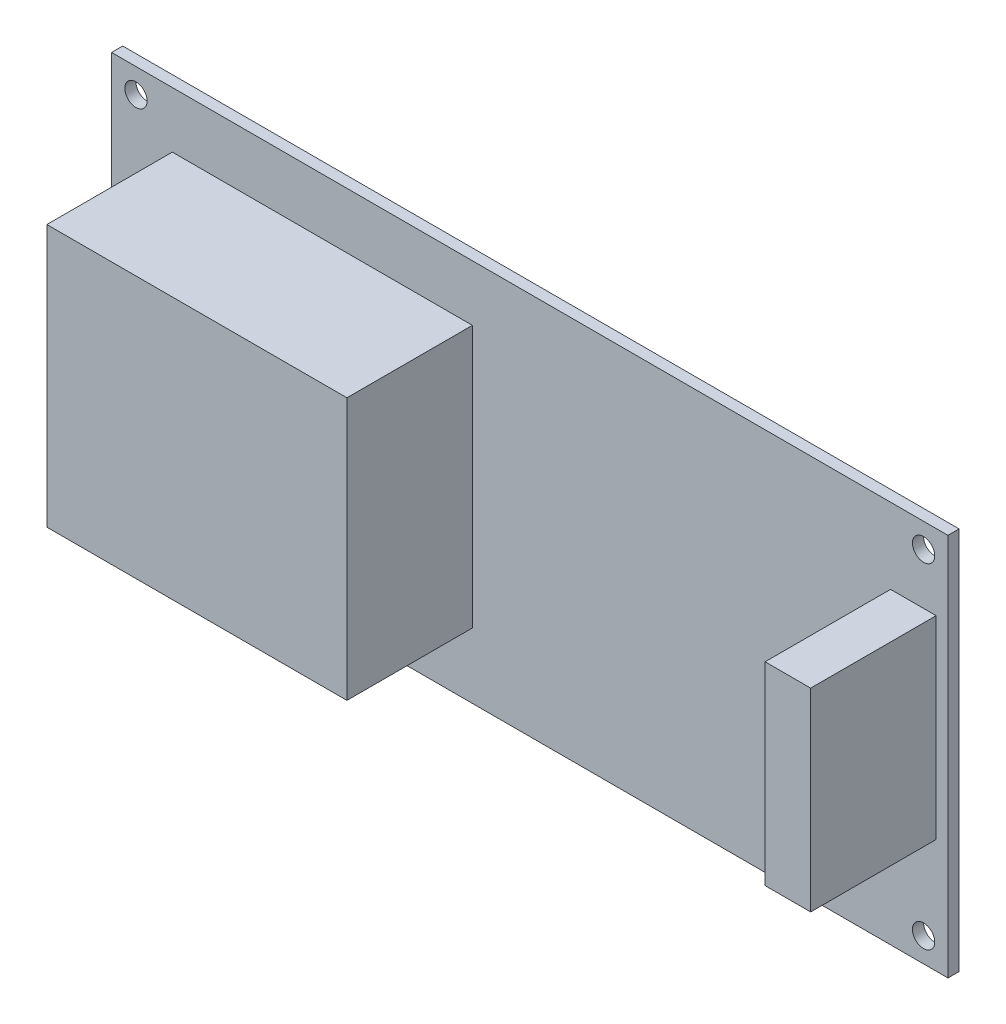
SolidWorks part; units mm, degrees
ref_plane "Plan de face" through (0, 0, 0) normal (0, 0, 1) x (1, 0, 0)
ref_plane "Plan de dessus" through (0, 0, 0) normal (0, 1, 0) x (1, 0, 0)
ref_plane "Plan de droite" through (0, 0, 0) normal (1, 0, 0) x (0, 0, -1)
sketch "Esquisse1" plane through (0, 0, 0) normal (0, 0, 1) x (1, 0, 0)
  line L0 (-56.5, 24) -> (56.5, -24) construction
  line L1 (-60, 27.5) -> (60, 27.5)
  line L2 (-60, 27.5) -> (-60, -27.5)
  line L3 (-60, -27.5) -> (60, -27.5)
  line L4 (60, 27.5) -> (60, -27.5)
  circle A0 centre (-56.5, 24) radius 1.6
  circle A1 centre (56.5, 24) radius 1.6
  circle A2 centre (56.5, -24) radius 1.6
  circle A3 centre (-56.5, -24) radius 1.6
  point P12 (0, 27.5)
  point P14 (-60, 0)
  point P15 (0, 0)
  point P16 (0, 0)
  point P17 (0, 0)
  point P18 (0, 0)
  point P19 (0, 0)
  point P20 (0, 0)
  dimension "D3" = 3.2
  dimension "D1" = 120
  dimension "D2" = 55
  dimension "D4" = 48
  dimension "D5" = 113
extrude "Boss.-Extru.1" add sketch "Esquisse1" along normal blind 1.6
sketch "Esquisse2" plane through (0, 0, 1.6) normal (0, 0, 1) x (1, 0, 0)
  line L1 (-51.2828, 19.4768) -> (-8.2325, 19.4768)
  line L2 (-51.2828, 19.4768) -> (-51.2828, -18.1267)
  line L3 (-51.2828, -18.1267) -> (-8.2325, -18.1267)
  line L4 (-8.2325, 19.4768) -> (-8.2325, -18.1267)
  line L5 (51.7605, 16.6697) -> (58.2997, 16.6697)
  line L6 (51.7605, 16.6697) -> (51.7605, -11.1452)
  line L7 (51.7605, -11.1452) -> (58.2997, -11.1452)
  line L8 (58.2997, 16.6697) -> (58.2997, -11.1452)
extrude "Boss.-Extru.2" add sketch "Esquisse2" along normal blind 18 contours L4 L1 L2 L3 | L6 L5 L8 L7
